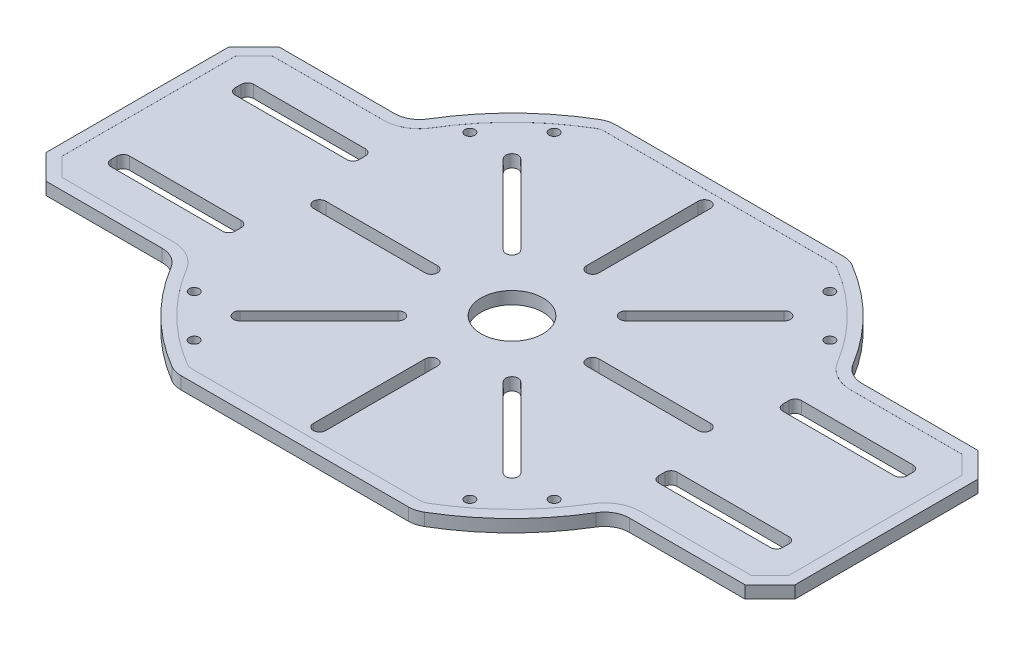
SolidWorks part; units mm, degrees
ref_plane "Front Plane" through (0, 0, 0) normal (0, 0, 1) x (1, 0, 0)
ref_plane "Top Plane" through (0, 0, 0) normal (0, 1, 0) x (1, 0, 0)
ref_plane "Right Plane" through (0, 0, 0) normal (1, 0, 0) x (0, 0, -1)
sketch "Sketch1" plane through (0, 0, 0) normal (0, 1, 0) x (1, 0, 0)
  line L0 (0, -1000) -> (0, 49000) construction
  line L1 (-23.2448, 44.45) -> (23.2448, 44.45)
  line L2 (-76.5969, 18.7325) -> (-76.5969, -18.7325)
  line L3 (-23.2448, -44.45) -> (23.2448, -44.45)
  line L4 (76.5969, 18.7325) -> (76.5969, -18.7325)
  line L6 (35.4178, 36.4243) -> (41.9684, 29.8736) construction
  line L7 (-76.5969, 0) -> (76.5969, 0) construction
  line L8 (-71.5169, 23.8125) -> (-47.8309, 23.8125)
  line L9 (-71.5169, -23.8125) -> (-47.8309, -23.8125)
  line L10 (-23.8125, 64.7529) -> (-23.8125, -44.45) construction
  line L11 (23.8125, 64.7529) -> (23.8125, -44.45) construction
  line L12 (47.8309, -23.8125) -> (71.5169, -23.8125)
  line L13 (47.8309, 23.8125) -> (71.5169, 23.8125)
  line L14 (-76.5969, -18.7325) -> (-71.5169, -23.8125)
  line L15 (-71.5169, 23.8125) -> (-76.5969, 18.7325)
  line L16 (71.5169, 23.8125) -> (76.5969, 18.7325)
  line L17 (71.5169, -23.8125) -> (76.5969, -18.7325)
  line L18 (707.1068, -707.1068) -> (-34648.2323, 34648.2323) construction
  line L19 (-707.1068, -707.1068) -> (34648.2323, 34648.2323) construction
  circle A0 centre (0, 0) radius 6.35
  arc A1 (-25.8276, 43.7444) -> (-43.4827, 26.2659) centre (0, 0) ccw
  arc A2 (25.8276, 43.7444) -> (23.2448, 44.45) centre (23.2448, 39.37) ccw
  arc A3 (-23.2448, 44.45) -> (-25.8276, 43.7444) centre (-23.2448, 39.37) ccw
  arc A4 (25.8276, -43.7444) -> (43.4827, -26.2659) centre (0, 0) ccw
  arc A5 (25.8276, -43.7444) -> (23.2448, -44.45) centre (23.2448, -39.37) cw
  arc A6 (-25.8276, -43.7444) -> (-23.2448, -44.45) centre (-23.2448, -39.37) ccw
  arc A7 (-43.4827, -26.2659) -> (-25.8276, -43.7444) centre (0, 0) ccw
  arc A8 (43.4827, 26.2659) -> (25.8276, 43.7444) centre (0, 0) ccw
  arc A9 (-47.8309, -23.8125) -> (-43.4827, -26.2659) centre (-47.8309, -28.8925) cw
  arc A10 (47.8309, -23.8125) -> (43.4827, -26.2659) centre (47.8309, -28.8925) ccw
  arc A11 (43.4827, 26.2659) -> (47.8309, 23.8125) centre (47.8309, 28.8925) ccw
  arc A12 (-47.8309, 23.8125) -> (-43.4827, 26.2659) centre (-47.8309, 28.8925) ccw
  circle A13 centre (36.8191, 28.198) radius 1.016
  circle A14 centre (28.198, 36.8191) radius 1.016
  circle A15 centre (26.6716, 26.6716) radius 0.081
  circle A16 centre (26.6716, -26.6716) radius 0.081
  circle A17 centre (36.8191, -28.198) radius 1.016
  circle A18 centre (28.198, -36.8191) radius 1.016
  circle A19 centre (-26.6716, -26.6716) radius 0.081
  circle A20 centre (-28.198, -36.8191) radius 1.016
  circle A21 centre (-36.8191, -28.198) radius 1.016
  circle A22 centre (-26.6716, 26.6716) radius 0.081
  circle A23 centre (-36.8191, 28.198) radius 1.016
  circle A24 centre (-28.198, 36.8191) radius 1.016
  point P0 (0, 0)
  point P8 (76.5969, -23.8125)
  point P11 (-76.5969, -23.8125)
  point P12 (-76.5969, 23.8125)
  point P34 (76.5969, 23.8125)
  point P81 (0, 0)
  dimension "D3" = 12.7
  dimension "D6" = 5.08
  dimension "D1" = 5.08
  dimension "D2" = 5.08
  dimension "D7" = 4.826
  dimension "D4" = 23.8125
  dimension "D5" = 23.8125
  dimension "D8" = 6.096
  dimension "D13" = 4
extrude "Boss-Extrude1" add sketch "Sketch1" along normal blind 2.54
sketch "Sketch3" plane through (0, 2.54, 0) normal (0, 1, 0) x (1, 0, 0)
  line L0 (0, 0) -> (46.2784, 46.2784) construction
  line L1 (10.7763, 12.5724) -> (26.9408, 28.7368)
  line L2 (16.51, -1.27) -> (39.37, -1.27)
  line L3 (16.51, 1.27) -> (39.37, 1.27)
  line L4 (12.5724, 10.7763) -> (28.7368, 26.9408)
  line L5 (10.5167, 12.1967) -> (28.9964, 27.3164) construction
  line L6 (19.7566, 19.7566) -> (12.1967, 10.5167) construction
  line L7 (35.921, 35.921) -> (38.568, 33.274) construction
  line L8 (10.7763, -12.5724) -> (26.9408, -28.7368)
  line L9 (12.5724, -10.7763) -> (28.7368, -26.9408)
  line L10 (-1.27, -16.51) -> (-1.27, -39.37)
  line L11 (1.27, -16.51) -> (1.27, -39.37)
  line L12 (-12.5724, -10.7763) -> (-28.7368, -26.9408)
  line L13 (-10.7763, -12.5724) -> (-26.9408, -28.7368)
  line L14 (-16.51, 1.27) -> (-39.37, 1.27)
  line L15 (-16.51, -1.27) -> (-39.37, -1.27)
  line L16 (-10.7763, 12.5724) -> (-26.9408, 28.7368)
  line L17 (-12.5724, 10.7763) -> (-28.7368, 26.9408)
  line L18 (1.27, 16.51) -> (1.27, 39.37)
  line L19 (-1.27, 16.51) -> (-1.27, 39.37)
  arc A0 (43.4827, 26.2659) -> (25.8276, 43.7444) centre (0, 0) ccw construction
  arc A1 (28.7368, 26.9408) -> (26.9408, 28.7368) centre (27.8388, 27.8388) ccw
  arc A2 (10.7763, 12.5724) -> (12.5724, 10.7763) centre (11.6743, 11.6743) ccw
  arc A3 (39.37, -1.27) -> (39.37, 1.27) centre (39.37, 0) ccw
  arc A4 (16.51, 1.27) -> (16.51, -1.27) centre (16.51, 0) ccw
  arc A5 (26.9408, -28.7368) -> (28.7368, -26.9408) centre (27.8388, -27.8388) ccw
  arc A6 (12.5724, -10.7763) -> (10.7763, -12.5724) centre (11.6743, -11.6743) ccw
  arc A7 (-1.27, -39.37) -> (1.27, -39.37) centre (0, -39.37) ccw
  arc A8 (1.27, -16.51) -> (-1.27, -16.51) centre (0, -16.51) ccw
  arc A9 (-28.7368, -26.9408) -> (-26.9408, -28.7368) centre (-27.8388, -27.8388) ccw
  arc A10 (-10.7763, -12.5724) -> (-12.5724, -10.7763) centre (-11.6743, -11.6743) ccw
  arc A11 (-39.37, 1.27) -> (-39.37, -1.27) centre (-39.37, 0) ccw
  arc A12 (-16.51, -1.27) -> (-16.51, 1.27) centre (-16.51, 0) ccw
  arc A13 (-26.9408, 28.7368) -> (-28.7368, 26.9408) centre (-27.8388, 27.8388) ccw
  arc A14 (-12.5724, 10.7763) -> (-10.7763, 12.5724) centre (-11.6743, 11.6743) ccw
  arc A15 (1.27, 39.37) -> (-1.27, 39.37) centre (0, 39.37) ccw
  arc A16 (-1.27, 16.51) -> (1.27, 16.51) centre (0, 16.51) ccw
  point P4 (19.7566, 19.7566)
  point P64 (0, 0)
  dimension "D1" = 8
  dimension "D3" = 1.27
extrude "Cut-Extrude1" cut sketch "Sketch3" against normal blind 2.54
sketch "Sketch4" plane through (0, 2.54, 0) normal (0, 1, 0) x (1, 0, 0)
  line L0 (-1000, 0) -> (49000, 0) construction
  line L1 (76.5969, -18.7325) -> (76.5969, 18.7325) construction
  line L2 (44.5929, 14.605) -> (67.4529, 14.605)
  line L3 (43.3229, 13.335) -> (43.3229, 12.065)
  line L4 (44.5929, 10.795) -> (67.4529, 10.795)
  line L5 (68.7229, 13.335) -> (68.7229, 12.065)
  line L6 (43.3229, 14.605) -> (68.7229, 10.795) construction
  line L7 (43.3229, 10.795) -> (68.7229, 14.605) construction
  line L8 (68.7229, -13.335) -> (68.7229, -12.065)
  line L9 (44.5929, -10.795) -> (67.4529, -10.795)
  line L10 (43.3229, -13.335) -> (43.3229, -12.065)
  line L11 (44.5929, -14.605) -> (67.4529, -14.605)
  line L12 (0, 0) -> (0, -50000) construction
  line L13 (-44.5929, -14.605) -> (-67.4529, -14.605)
  line L14 (-43.3229, -13.335) -> (-43.3229, -12.065)
  line L15 (-44.5929, -10.795) -> (-67.4529, -10.795)
  line L16 (-68.7229, -13.335) -> (-68.7229, -12.065)
  line L17 (-43.3229, 10.795) -> (-68.7229, 14.605) construction
  line L18 (-43.3229, 14.605) -> (-68.7229, 10.795) construction
  line L19 (-68.7229, 13.335) -> (-68.7229, 12.065)
  line L20 (-44.5929, 10.795) -> (-67.4529, 10.795)
  line L21 (-43.3229, 13.335) -> (-43.3229, 12.065)
  line L22 (-44.5929, 14.605) -> (-67.4529, 14.605)
  arc A0 (44.5929, 10.795) -> (43.3229, 12.065) centre (44.5929, 12.065) cw
  arc A1 (43.3229, 13.335) -> (44.5929, 14.605) centre (44.5929, 13.335) cw
  arc A2 (68.7229, 12.065) -> (67.4529, 10.795) centre (67.4529, 12.065) cw
  arc A3 (68.7229, 13.335) -> (67.4529, 14.605) centre (67.4529, 13.335) ccw
  arc A4 (68.7229, -12.065) -> (67.4529, -10.795) centre (67.4529, -12.065) ccw
  arc A5 (68.7229, -13.335) -> (67.4529, -14.605) centre (67.4529, -13.335) cw
  arc A6 (44.5929, -10.795) -> (43.3229, -12.065) centre (44.5929, -12.065) ccw
  arc A7 (43.3229, -13.335) -> (44.5929, -14.605) centre (44.5929, -13.335) ccw
  arc A8 (-43.3229, -13.335) -> (-44.5929, -14.605) centre (-44.5929, -13.335) cw
  arc A9 (-44.5929, -10.795) -> (-43.3229, -12.065) centre (-44.5929, -12.065) cw
  arc A10 (-68.7229, -13.335) -> (-67.4529, -14.605) centre (-67.4529, -13.335) ccw
  arc A11 (-68.7229, -12.065) -> (-67.4529, -10.795) centre (-67.4529, -12.065) cw
  arc A12 (-68.7229, 13.335) -> (-67.4529, 14.605) centre (-67.4529, 13.335) cw
  arc A13 (-68.7229, 12.065) -> (-67.4529, 10.795) centre (-67.4529, 12.065) ccw
  arc A14 (-43.3229, 13.335) -> (-44.5929, 14.605) centre (-44.5929, 13.335) ccw
  arc A15 (-44.5929, 10.795) -> (-43.3229, 12.065) centre (-44.5929, 12.065) ccw
  point P1 (56.0229, 12.7)
  point P64 (-56.0229, 12.7)
  dimension "D5" = 1.27
  dimension "D1" = 25.4
  dimension "D2" = 3.81
  dimension "D3" = 7.874
  dimension "D4" = 10.795
extrude "Cut-Extrude2" cut sketch "Sketch4" against normal blind 2.54
sketch "Sketch8" plane through (0, 2.54, 0) normal (0, 1, 0) x (1, 0, 0)
  line L12 (47.8309, -23.8125) -> (71.5169, -23.8125)
  line L13 (71.5169, -23.8125) -> (76.5969, -18.7325)
  line L14 (76.5969, -18.7325) -> (76.5969, 18.7325)
  line L15 (76.5969, 18.7325) -> (71.5169, 23.8125)
  line L16 (71.5169, 23.8125) -> (47.8309, 23.8125)
  line L17 (23.2448, 44.45) -> (-23.2448, 44.45)
  line L18 (-47.8309, 23.8125) -> (-71.5169, 23.8125)
  line L19 (-71.5169, 23.8125) -> (-76.5969, 18.7325)
  line L20 (-76.5969, 18.7325) -> (-76.5969, -18.7325)
  line L21 (-76.5969, -18.7325) -> (-71.5169, -23.8125)
  line L22 (-71.5169, -23.8125) -> (-47.8309, -23.8125)
  line L23 (-23.2448, -44.45) -> (23.2448, -44.45)
  line L24 (47.8309, -21.5125) -> (70.5642, -21.5125)
  line L25 (70.5642, -21.5125) -> (74.2969, -17.7798)
  line L26 (74.2969, -17.7798) -> (74.2969, 17.7798)
  line L27 (74.2969, 17.7798) -> (70.5642, 21.5125)
  line L28 (70.5642, 21.5125) -> (47.8309, 21.5125)
  line L29 (23.2448, 42.15) -> (-23.2448, 42.15)
  line L30 (-47.8309, 21.5125) -> (-70.5642, 21.5125)
  line L31 (-70.5642, 21.5125) -> (-74.2969, 17.7798)
  line L32 (-74.2969, 17.7798) -> (-74.2969, -17.7798)
  line L33 (-74.2969, -17.7798) -> (-70.5642, -21.5125)
  line L34 (-70.5642, -21.5125) -> (-47.8309, -21.5125)
  line L35 (-23.2448, -42.15) -> (23.2448, -42.15)
  line L36 (47.8309, -21.5125) -> (70.5642, -21.5125)
  line L37 (70.5642, -21.5125) -> (74.2969, -17.7798)
  line L38 (74.2969, -17.7798) -> (74.2969, 17.7798)
  line L39 (74.2969, 17.7798) -> (70.5642, 21.5125)
  line L40 (70.5642, 21.5125) -> (47.8309, 21.5125)
  line L41 (23.2448, 42.15) -> (-23.2448, 42.15)
  line L42 (-47.8309, 21.5125) -> (-70.5642, 21.5125)
  line L43 (-70.5642, 21.5125) -> (-74.2969, 17.7798)
  line L44 (-74.2969, 17.7798) -> (-74.2969, -17.7798)
  line L45 (-74.2969, -17.7798) -> (-70.5642, -21.5125)
  line L46 (-70.5642, -21.5125) -> (-47.8309, -21.5125)
  line L47 (-23.2448, -42.15) -> (23.2448, -42.15)
  arc A12 (23.2448, -44.45) -> (25.8276, -43.7444) centre (23.2448, -39.37) ccw
  arc A13 (25.8276, -43.7444) -> (43.4827, -26.2659) centre (0, 0) ccw
  arc A14 (47.8309, -23.8125) -> (43.4827, -26.2659) centre (47.8309, -28.8925) ccw
  arc A15 (43.4827, 26.2659) -> (47.8309, 23.8125) centre (47.8309, 28.8925) ccw
  arc A16 (43.4827, 26.2659) -> (25.8276, 43.7444) centre (0, 0) ccw
  arc A17 (25.8276, 43.7444) -> (23.2448, 44.45) centre (23.2448, 39.37) ccw
  arc A18 (-23.2448, 44.45) -> (-25.8276, 43.7444) centre (-23.2448, 39.37) ccw
  arc A19 (-25.8276, 43.7444) -> (-43.4827, 26.2659) centre (0, 0) ccw
  arc A20 (-47.8309, 23.8125) -> (-43.4827, 26.2659) centre (-47.8309, 28.8925) ccw
  arc A21 (-43.4827, -26.2659) -> (-47.8309, -23.8125) centre (-47.8309, -28.8925) ccw
  arc A22 (-43.4827, -26.2659) -> (-25.8276, -43.7444) centre (0, 0) ccw
  arc A23 (-25.8276, -43.7444) -> (-23.2448, -44.45) centre (-23.2448, -39.37) ccw
  arc A24 (23.2448, -42.15) -> (24.6582, -41.7639) centre (23.2448, -39.37) ccw
  arc A25 (24.6582, -41.7639) -> (41.514, -25.0767) centre (0, 0) ccw
  arc A26 (47.8309, -21.5125) -> (41.514, -25.0767) centre (47.8309, -28.8925) ccw
  arc A27 (41.514, 25.0767) -> (47.8309, 21.5125) centre (47.8309, 28.8925) ccw
  arc A28 (41.514, 25.0767) -> (24.6582, 41.7639) centre (0, 0) ccw
  arc A29 (24.6582, 41.7639) -> (23.2448, 42.15) centre (23.2448, 39.37) ccw
  arc A30 (-23.2448, 42.15) -> (-24.6582, 41.7639) centre (-23.2448, 39.37) ccw
  arc A31 (-24.6582, 41.7639) -> (-41.514, 25.0767) centre (0, 0) ccw
  arc A32 (-47.8309, 21.5125) -> (-41.514, 25.0767) centre (-47.8309, 28.8925) ccw
  arc A33 (-41.514, -25.0767) -> (-47.8309, -21.5125) centre (-47.8309, -28.8925) ccw
  arc A34 (-41.514, -25.0767) -> (-24.6582, -41.7639) centre (0, 0) ccw
  arc A35 (-24.6582, -41.7639) -> (-23.2448, -42.15) centre (-23.2448, -39.37) ccw
  arc A36 (23.2448, -42.15) -> (24.6582, -41.7639) centre (23.2448, -39.37) ccw
  arc A37 (24.6582, -41.7639) -> (41.514, -25.0767) centre (0, 0) ccw
  arc A38 (47.8309, -21.5125) -> (41.514, -25.0767) centre (47.8309, -28.8925) ccw
  arc A39 (41.514, 25.0767) -> (47.8309, 21.5125) centre (47.8309, 28.8925) ccw
  arc A40 (41.514, 25.0767) -> (24.6582, 41.7639) centre (0, 0) ccw
  arc A41 (24.6582, 41.7639) -> (23.2448, 42.15) centre (23.2448, 39.37) ccw
  arc A42 (-23.2448, 42.15) -> (-24.6582, 41.7639) centre (-23.2448, 39.37) ccw
  arc A43 (-24.6582, 41.7639) -> (-41.514, 25.0767) centre (0, 0) ccw
  arc A44 (-47.8309, 21.5125) -> (-41.514, 25.0767) centre (-47.8309, 28.8925) ccw
  arc A45 (-41.514, -25.0767) -> (-47.8309, -21.5125) centre (-47.8309, -28.8925) ccw
  arc A46 (-41.514, -25.0767) -> (-24.6582, -41.7639) centre (0, 0) ccw
  arc A47 (-24.6582, -41.7639) -> (-23.2448, -42.15) centre (-23.2448, -39.37) ccw
  dimension "D1" = 2.3
  dimension "D2" = 2.3
extrude "Boss-Extrude2" add sketch "Sketch8" along normal blind 0.01
